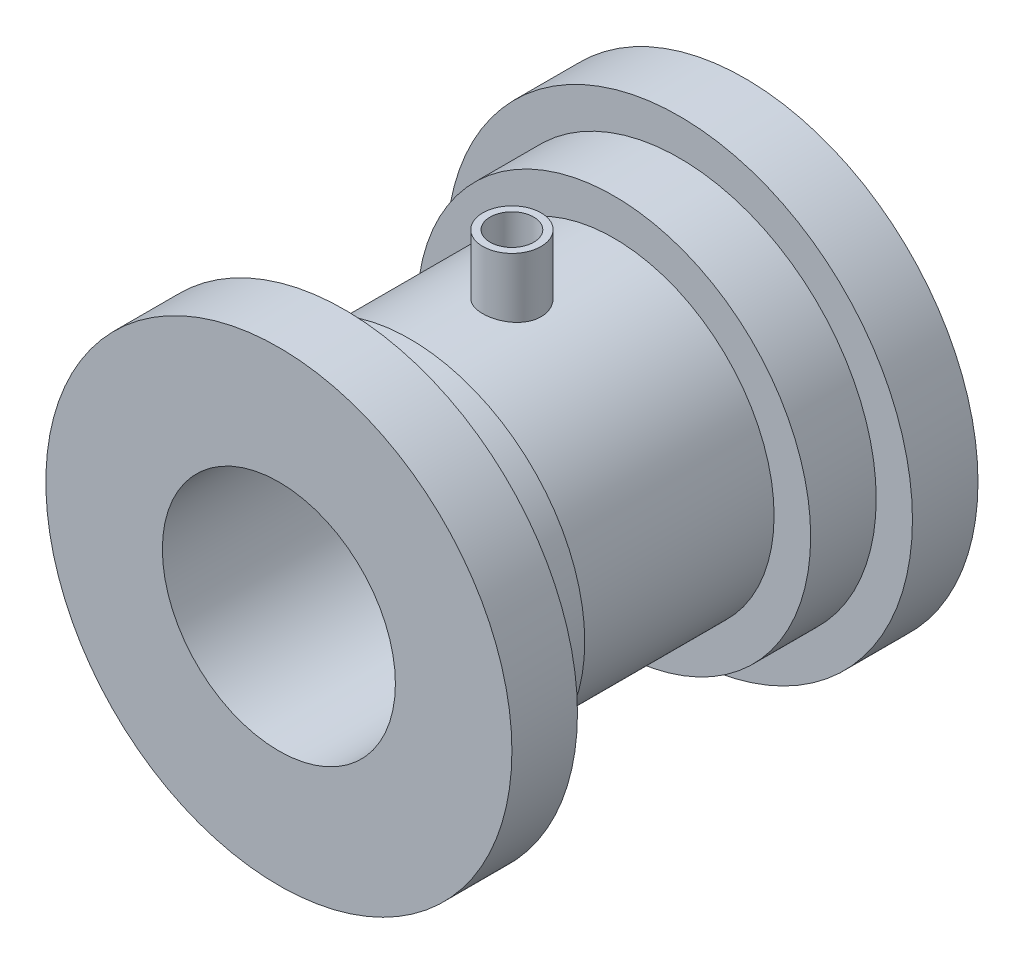
SolidWorks part; units mm, degrees
ref_plane "Front Plane" through (0, 0, 0) normal (0, 0, 1) x (1, 0, 0)
ref_plane "Top Plane" through (0, 0, 0) normal (0, 1, 0) x (1, 0, 0)
ref_plane "Right Plane" through (0, 0, 0) normal (1, 0, 0) x (0, 0, -1)
sketch "Sketch1" plane through (0, 0, 0) normal (1, 0, 0) x (0, 0, -1)
  line L0 (0, 0) -> (40876.5529, 0) construction
  line L1 (-22.9854, 16) -> (-22.9854, 32)
  line L2 (-22.9854, 32) -> (-13.9854, 32)
  line L3 (-13.9854, 32) -> (-13.9854, 24)
  line L4 (-13.9854, 24) -> (-4.9854, 24)
  line L5 (-4.9854, 24) -> (-4.9854, 22)
  line L6 (-4.9854, 22) -> (23.0146, 22)
  line L7 (23.0146, 22) -> (23.0146, 27.0224)
  line L8 (23.0146, 27.0224) -> (32.0146, 27.0224)
  line L9 (32.0146, 27.0224) -> (32.0146, 32)
  line L10 (32.0146, 32) -> (41.0146, 32)
  line L11 (41.0146, 32) -> (41.0146, 16)
  line L12 (41.0146, 16) -> (-22.9854, 16)
  dimension "D1" = 46
  dimension "D2" = 9
  dimension "D3" = 9
  dimension "D4" = 28
  dimension "D5" = 16
  dimension "D6" = 22
  dimension "D7" = 24
  dimension "D8" = 32
revolve "Revolve1" add sketch "Sketch1" angle 360 about L0
sketch "Sketch2" plane through (0, 0, 0) normal (0, 1, 0) x (1, 0, 0)
  line L1 (0, 41.0146) -> (0, -44.308) construction
  line L2 (16, 41.0146) -> (-16, 41.0146) construction
  line L3 (-22, 9.0146) -> (30.8516, 9.0146) construction
  line L4 (-22, 23.0146) -> (-22, -4.9854) construction
  circle A0 centre (0, 9.0146) radius 3
  point P11 (0, 0)
  dimension "D1" = 6
sketch "Sketch3" plane through (0, 0, 0) normal (0, 1, 0) x (1, 0, 0)
  circle A0 centre (0, 9.0146) radius 4
  point P3 (0, 0)
  point P4 (0, 0)
  dimension "D1" = 8
extrude "Boss-Extrude1" add sketch "Sketch3" along normal blind 8 from offset 22
sketch "Sketch4" plane through (0, 22, 0) normal (0, -1, 0) x (1, 0, 0)
  circle A1 centre (0, -9.0146) radius 4
  circle A2 centre (0, -9.0146) radius 4
  dimension "D1" = 0
extrude "Boss-Extrude2" add sketch "Sketch4" along normal up to surface
extrude "Cut-Extrude2" cut sketch "Sketch2" against normal through all both and the other way through all contours A0
